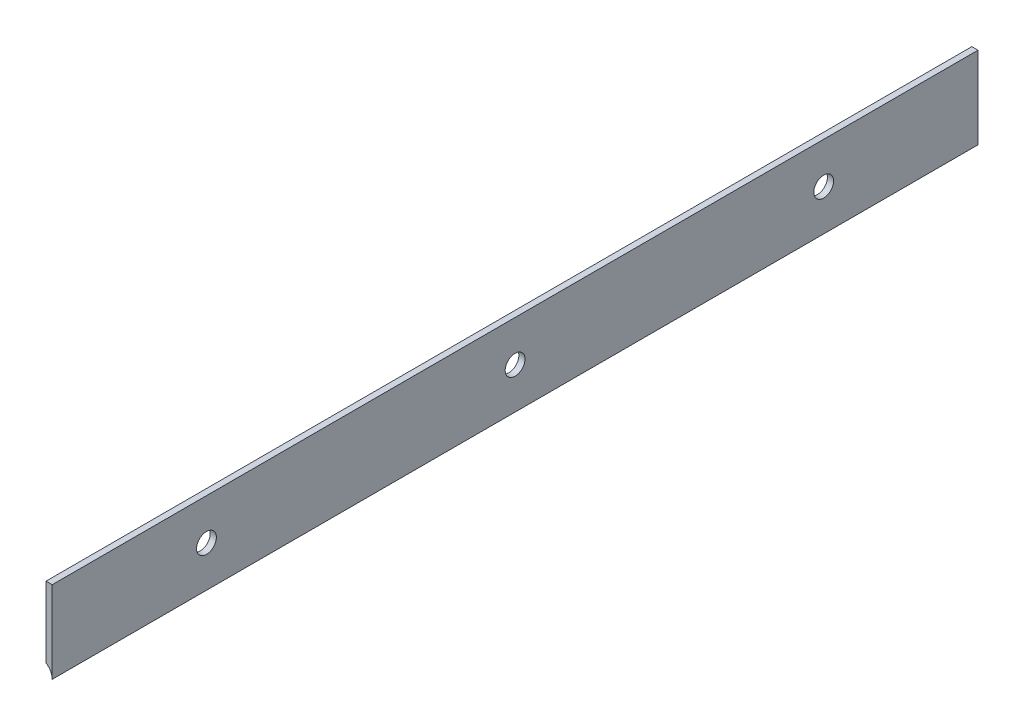
SolidWorks part; units mm, degrees
material "6061-T6 (SS)"
ref_plane "Front Plane" through (0, 0, 0) normal (0, 0, 1) x (1, 0, 0)
ref_plane "Top Plane" through (0, 0, 0) normal (0, 1, 0) x (1, 0, 0)
ref_plane "Right Plane" through (0, 0, 0) normal (1, 0, 0) x (0, 0, -1)
sketch "Sketch2" plane through (0, 0, 0) normal (0, 0, 1) x (1, 0, 0)
  line L2 (-0.508, -4.9153) -> (-0.508, 6.7469)
  line L3 (-0.508, 6.7469) -> (0.508, 6.7469)
  line L4 (0.508, -6.7469) -> (0.508, 6.7469)
  line L5 (-0.3768, -5.004) -> (0.508, 6.7469) construction
  line L6 (-0.508, 6.7469) -> (0.508, -6.7469) construction
  arc A0 (0.508, -6.7469) -> (-0.508, -4.9153) centre (-1.651, -6.7469) ccw
  point P0 (0, 0)
  dimension "D3" = 4.318
  dimension "D1" = 13.4937
  dimension "D2" = 1.016
extrude "Boss-Extrude3" add sketch "Sketch2" along normal blind 152.4
hole_wizard "#4 Clearance Hole2" positions "Sketch6" profile "Sketch5" hole size "#4" standard "ANSI Inch"
sketch "Sketch6" plane through (0.508, 0, 0) normal (1, 0, 0) x (0, 0, -1)
  point P0 (-25.4, 0)
  point P3 (-76.2, 0)
  point P6 (-177.8, 0)
  point P9 (-127, 0)
  point P12 (-228.6, 0)
  point P15 (-279.4, 0)
sketch "Sketch5" plane through (0.508, 0, 25.4) normal (0, 1, 0) x (0, 0, -1)
  line L0 (0, 0) -> (0, 2.5046)
  line L1 (0, 2.5046) -> (1.6319, 1.524)
  line L2 (1.6319, 1.524) -> (1.6319, 0)
  line L5 (1.6319, 0) -> (0, 0)
  line L10 (0, 2.5046) -> (-1.6319, 1.524) construction
  line L11 (0, -6.35) -> (0, 107.95) construction
  dimension "Hole Dia." = 3.2639
  dimension "Hole Depth" = 1.524
  dimension "Drill Angle" = 118
